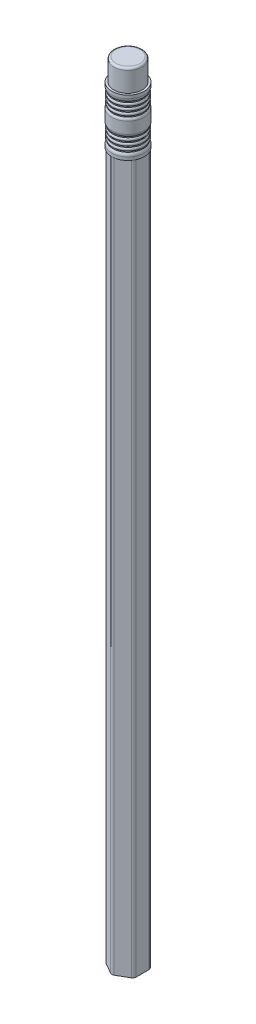
SolidWorks part; units mm, degrees
ref_plane "Front Plane" through (0, 0, 0) normal (0, 0, 1) x (1, 0, 0)
ref_plane "Top Plane" through (0, 0, 0) normal (0, 1, 0) x (1, 0, 0)
ref_plane "Right Plane" through (0, 0, 0) normal (1, 0, 0) x (0, 0, -1)
sketch "Sketch1" plane through (0, 0, 0) normal (0, 1, 0) x (1, 0, 0)
  circle A0 centre (0, 0) radius 0.9398
  dimension "D1" = 1.8796
extrude "Extrude1" add sketch "Sketch1" along normal blind 177.8
sketch "Sketch2" plane through (0, 0, 0) normal (0, 1, 0) x (1, 0, 0)
  line L1 (0.381, -3.8128) -> (3.1115, -2.2364)
  line L2 (3.4925, -1.5765) -> (3.4925, 1.5765)
  line L3 (3.1115, 2.2364) -> (0.381, 3.8128)
  line L4 (-0.381, 3.8128) -> (-3.1115, 2.2364)
  line L5 (-3.4925, 1.5765) -> (-3.4925, -1.5765)
  line L6 (-3.1115, -2.2364) -> (-0.381, -3.8128)
  circle A0 centre (0, 0) radius 0.9525
  circle A1 centre (0, 0) radius 3.4925 construction
  arc A2 (-3.4925, -1.5765) -> (-3.1115, -2.2364) centre (-2.7305, -1.5765) ccw
  arc A3 (0.381, -3.8128) -> (-0.381, -3.8128) centre (0, -3.1529) cw
  arc A4 (3.1115, -2.2364) -> (3.4925, -1.5765) centre (2.7305, -1.5765) ccw
  arc A5 (3.4925, 1.5765) -> (3.1115, 2.2364) centre (2.7305, 1.5765) ccw
  arc A6 (0.381, 3.8128) -> (-0.381, 3.8128) centre (0, 3.1529) ccw
  arc A7 (-3.1115, 2.2364) -> (-3.4925, 1.5765) centre (-2.7305, 1.5765) ccw
  dimension "D1" = 1.905
  dimension "D3" = 0.762
  dimension "D2" = 6.985
extrude "Extrude2" add sketch "Sketch2" along normal blind 171.45
sketch "Sketch3" plane through (0, 0, 0) normal (1, 0, 0) x (0, 0, -1)
  line L0 (3.6576, 172.974) -> (3.6576, 173.228)
  line L1 (3.6576, 173.99) -> (3.6576, 174.244)
  line L2 (3.6576, 175.006) -> (3.6576, 175.26)
  line L3 (3.937, 176.911) -> (3.937, 179.705)
  line L4 (3.6576, 176.022) -> (3.6576, 176.276)
  line L5 (3.6576, 180.34) -> (3.6576, 180.594)
  line L6 (3.6576, 181.356) -> (3.6576, 181.61)
  line L7 (3.6576, 182.372) -> (3.6576, 182.626)
  line L8 (3.6576, 183.388) -> (3.6576, 183.642)
  line L9 (3.937, 184.404) -> (3.937, 185.166)
  line L10 (3.937, 172.212) -> (3.937, 171.45)
  line L11 (0.9525, 171.45) -> (3.937, 171.45)
  line L12 (0.9525, 171.45) -> (0.9398, 185.166)
  line L13 (0.9398, 0) -> (0.9398, 177.8) construction
  line L14 (3.9149, 0) -> (3.9149, 171.45) construction
  line L15 (0, 0) -> (0, 231.8167) construction
  line L16 (0.9398, 185.166) -> (3.937, 185.166)
  arc A0 (3.937, 172.212) -> (3.6576, 172.974) centre (2.7582, 172.212) ccw
  arc A1 (3.6576, 173.228) -> (3.6576, 173.99) centre (3.402, 173.609) ccw
  arc A2 (3.6576, 174.244) -> (3.6576, 175.006) centre (3.402, 174.625) ccw
  arc A3 (3.6576, 175.26) -> (3.6576, 176.022) centre (3.402, 175.641) ccw
  arc A4 (3.6576, 176.276) -> (3.937, 176.911) centre (3.0757, 176.911) ccw
  arc A5 (3.937, 179.705) -> (3.6576, 180.34) centre (3.0757, 179.705) ccw
  arc A6 (3.6576, 180.594) -> (3.6576, 181.356) centre (3.402, 180.975) ccw
  arc A7 (3.6576, 181.61) -> (3.6576, 182.372) centre (3.402, 181.991) ccw
  arc A8 (3.6576, 182.626) -> (3.6576, 183.388) centre (3.402, 183.007) ccw
  arc A9 (3.6576, 183.642) -> (3.937, 184.404) centre (2.7582, 184.404) ccw
  point P30 (3.8608, 183.007)
  point P33 (3.9149, 171.45)
  dimension "D1" = 0.254
  dimension "D2" = 1.016
  dimension "D3" = 0.2032
  dimension "D4" = 3.937
  dimension "D5" = 0.0221
  dimension "D6" = 1.524
  dimension "D7" = 13.716
  dimension "D8" = 0.762
  dimension "D9" = 2.794
  dimension "D10" = 0.0762
revolve "Revolve1" add sketch "Sketch3" angle 360 about L15
sketch "Sketch4" plane through (0, 177.8, 0) normal (0, 1, 0) x (1, 0, 0)
  circle A0 centre (0, 0) radius 3.429
  dimension "D1" = 6.858
extrude "Extrude3" add sketch "Sketch4" along normal blind 12.7
fillet "Fillet1" radius 0.508 1 edges at (0, 190.5, 3.429)
